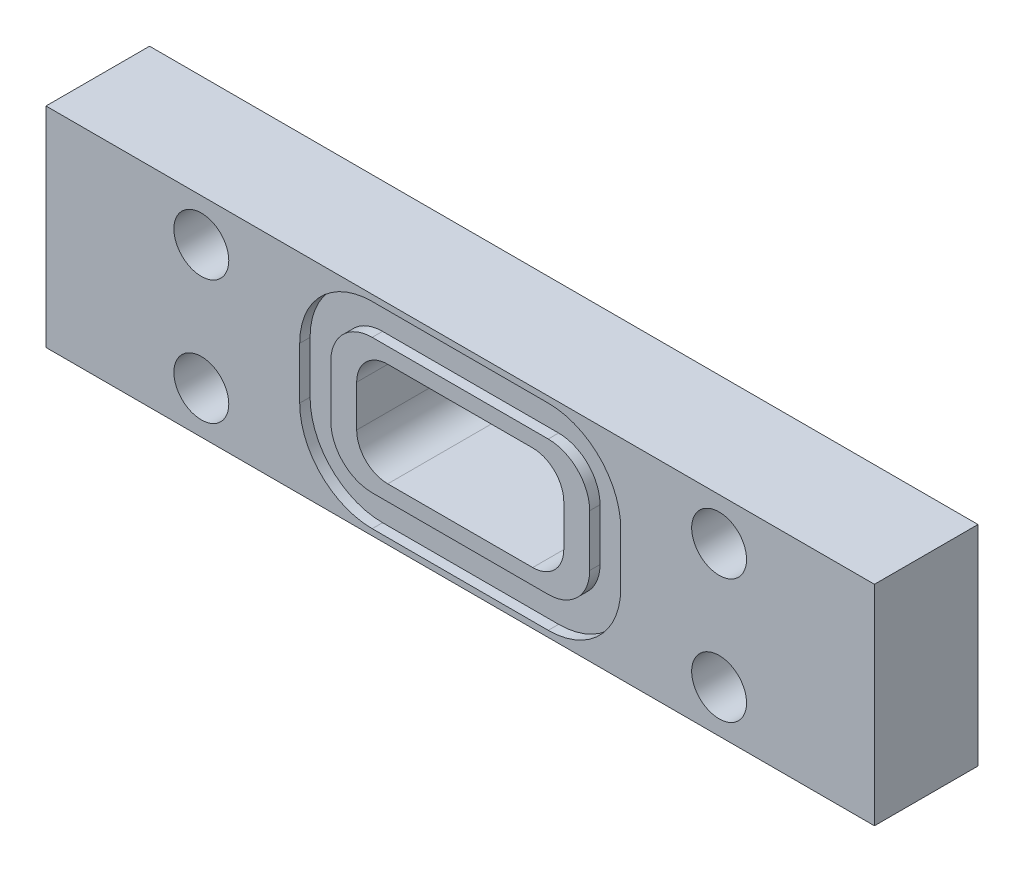
SolidWorks part; units mm, degrees
material "ABS PC"
ref_plane "Ebene vorne" through (0, 0, 0) normal (0, 0, 1) x (1, 0, 0)
ref_plane "Ebene oben" through (0, 0, 0) normal (0, 1, 0) x (1, 0, 0)
ref_plane "Ebene rechts" through (0, 0, 0) normal (1, 0, 0) x (0, 0, -1)
sketch "Skizze1" plane through (0, 0, 0) normal (0, 0, 1) x (1, 0, 0)
  line L0 (0, 10.1) -> (80, 10.1) construction
  line L1 (0, 0) -> (80, 0)
  line L2 (0, 0) -> (0, 20.2)
  line L3 (0, 20.2) -> (80, 20.2)
  line L4 (80, 0) -> (80, 20.2)
  line L5 (40, 20.2) -> (40, 0) construction
  line L7 (30, 15.1) -> (50, 15.1)
  line L8 (30, 15.1) -> (30, 5.1)
  line L9 (30, 5.1) -> (50, 5.1)
  line L10 (50, 15.1) -> (50, 5.1)
  line L11 (30, 15.1) -> (50, 5.1) construction
  line L12 (30, 5.1) -> (50, 15.1) construction
  line L13 (65, 4.1) -> (15, 4.1) construction
  line L14 (65, 4.1) -> (65, 16.1) construction
  line L15 (65, 16.1) -> (15, 16.1) construction
  line L16 (15, 4.1) -> (15, 16.1) construction
  line L17 (65, 4.1) -> (15, 16.1) construction
  line L18 (65, 16.1) -> (15, 4.1) construction
  circle A0 centre (15, 16.1) radius 2.65
  circle A1 centre (15, 4.1) radius 2.65
  circle A2 centre (65, 16.1) radius 2.65
  circle A3 centre (65, 4.1) radius 2.65
  point P9 (40, 10.1)
  point P14 (40, 10.1)
  dimension "D7" = 5.3
  dimension "D1" = 20.2
  dimension "D2" = 80
  dimension "D3" = 10
  dimension "D4" = 20
  dimension "D5" = 12
  dimension "D6" = 50
extrude "Aufsatz-Linear austragen1" add sketch "Skizze1" along normal blind 10
fillet "Verrundung1" radius 3 4 edges at (50, 5.1, 5) (30, 5.1, 5) (50, 15.1, 5) (30, 15.1, 5)
sketch "Skizze2" plane through (0, 0, 10) normal (0, 0, 1) x (1, 0, 0)
  line L0 (33, 5.1) -> (47, 5.1) construction
  line L5 (48.5, 16.6) -> (31.5, 16.6)
  line L6 (52.5, 12.6) -> (52.5, 7.6)
  line L7 (48.5, 3.6) -> (31.5, 3.6)
  line L8 (27.5, 12.6) -> (27.5, 7.6)
  line L9 (52.5, 16.6) -> (27.5, 3.6) construction
  line L10 (52.5, 3.6) -> (27.5, 16.6) construction
  line L11 (30, 12.1) -> (30, 8.1) construction
  line L12 (47, 15.1) -> (33, 15.1) construction
  line L13 (55.5, 12.6) -> (55.5, 7.6)
  line L14 (48.5, 0.6) -> (31.5, 0.6)
  line L15 (24.5, 12.6) -> (24.5, 7.6)
  line L16 (48.5, 19.6) -> (31.5, 19.6)
  arc A0 (48.5, 16.6) -> (52.5, 12.6) centre (48.5, 12.6) cw
  arc A1 (52.5, 7.6) -> (48.5, 3.6) centre (48.5, 7.6) cw
  arc A2 (31.5, 3.6) -> (27.5, 7.6) centre (31.5, 7.6) cw
  arc A3 (31.5, 16.6) -> (27.5, 12.6) centre (31.5, 12.6) ccw
  arc A4 (55.5, 7.6) -> (48.5, 0.6) centre (48.5, 7.6) cw
  arc A5 (31.5, 0.6) -> (24.5, 7.6) centre (31.5, 7.6) cw
  arc A6 (31.5, 19.6) -> (24.5, 12.6) centre (31.5, 12.6) ccw
  arc A7 (48.5, 19.6) -> (55.5, 12.6) centre (48.5, 12.6) cw
  point P0 (40, 10.1)
  point P5 (0, 0)
  point P8 (40, 5.1)
  point P9 (0, 0)
  point P12 (30, 10.1)
  dimension "D3" = 4
  dimension "D1" = 25
  dimension "D2" = 1.5
  dimension "D4" = 3
extrude "Schnitt-Linear austragen1" cut sketch "Skizze2" against normal blind 1
